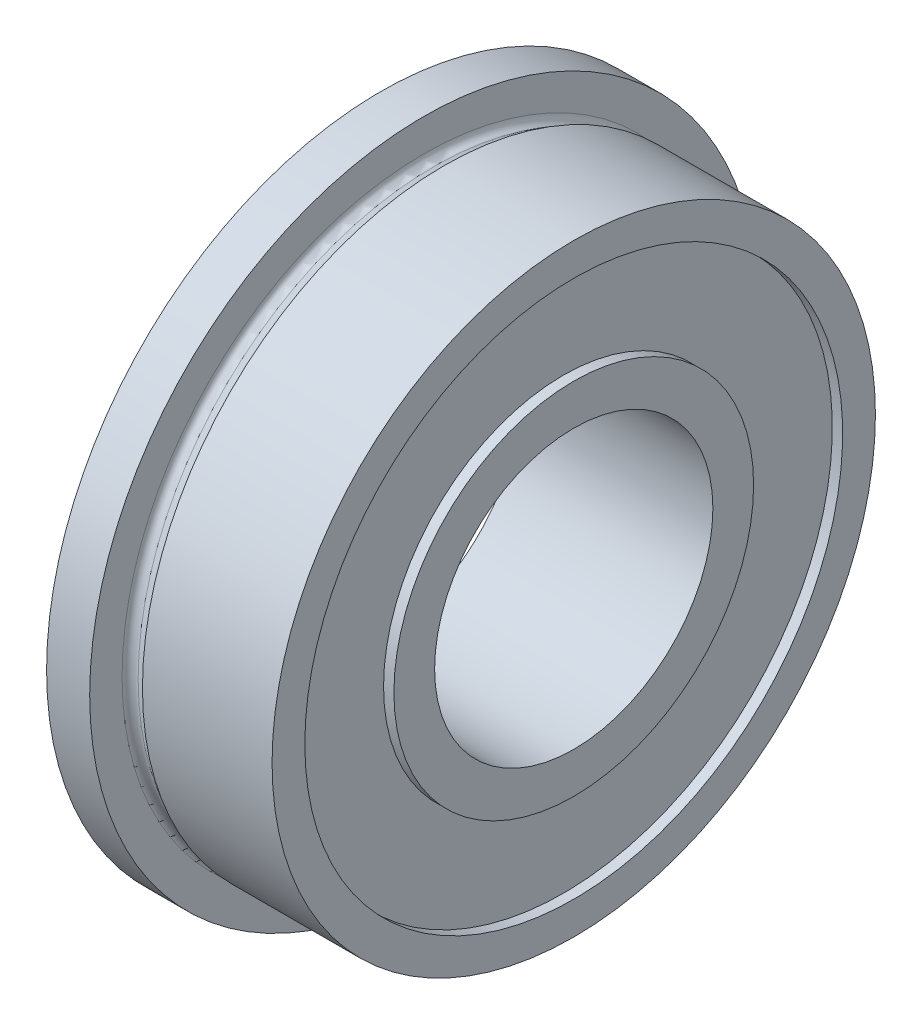
SolidWorks part; units mm, degrees
ref_plane "Front Plane" through (0, 0, 0) normal (0, 0, 1) x (1, 0, 0)
ref_plane "Top Plane" through (0, 0, 0) normal (0, 1, 0) x (1, 0, 0)
ref_plane "Right Plane" through (0, 0, 0) normal (1, 0, 0) x (0, 0, -1)
ref_plane "Plane1" through (0, 0, 0) normal (0, 0, -1) x (-1, 0, 0)
sketch "Sketch1" plane through (0, 0, 0) normal (0, 0, -1) x (-1, 0, 0)
  line L0 (-2.3375, 11.1125) -> (-7.112, 11.1125)
  line L1 (-7.112, 11.1125) -> (-7.112, 9.906)
  line L2 (-7.112, 9.906) -> (-6.731, 9.906)
  line L3 (-6.731, 9.906) -> (-6.731, 6.625)
  line L4 (-6.731, 6.625) -> (-7.112, 6.625)
  line L5 (-7.112, 6.625) -> (-7.112, 5.125)
  line L6 (-7.112, 5.125) -> (0, 5.125)
  line L7 (0, 5.125) -> (0, 6.625)
  line L8 (0, 6.625) -> (-0.381, 6.625)
  line L9 (-0.381, 6.625) -> (-0.381, 9.906)
  line L10 (-0.381, 9.906) -> (0, 9.906)
  line L11 (0, 9.906) -> (0, 12.3063)
  line L12 (0, 12.3063) -> (-1.5875, 12.3063)
  line L13 (-1.5875, 12.3063) -> (-1.5875, 11.1125)
  line L14 (-1.9625, 10.896) -> (-2.3375, 11.1125)
  line L15 (-7.112, 0) -> (0, 0) construction
  arc A0 (-1.5875, 11.1125) -> (-1.9625, 10.896) centre (-1.8375, 11.1125) cw
revolve "Revolve1" add sketch "Sketch1" angle 360 about L15
